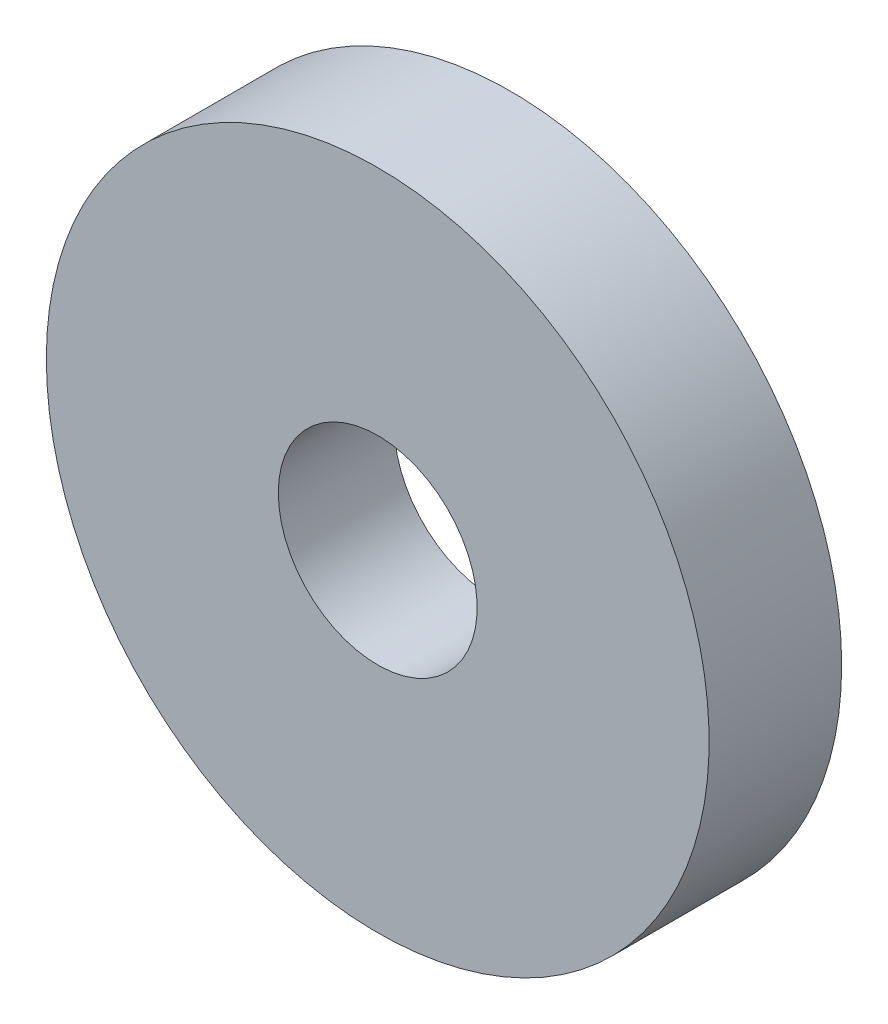
SolidWorks part; units mm, degrees
material "AISI 1020"
ref_plane "Спереди" through (0, 0, 0) normal (0, 0, 1) x (1, 0, 0)
ref_plane "Сверху" through (0, 0, 0) normal (0, 1, 0) x (1, 0, 0)
ref_plane "Справа" through (0, 0, 0) normal (1, 0, 0) x (0, 0, -1)
sketch "Эскиз1" plane through (0, 0, 0) normal (0, 0, 1) x (1, 0, 0)
  circle A0 centre (0, 0) radius 7.9 construction
  circle A1 centre (0, 0) radius 7.9
  circle A2 centre (0, 0) radius 20
  arc A3 (19.3591, 5.0223) -> (-19.3591, 5.0223) centre (0, 0) ccw construction
extrude "Бобышка-Вытянуть1" add sketch "Эскиз1" along normal up to surface (1 mm away)
sketch "Эскиз2" plane through (0, 0, 1) normal (0, 0, 1) x (1, 0, 0)
  circle A0 centre (0, 0) radius 6 construction
  circle A1 centre (0, 0) radius 6
  circle A2 centre (0, 0) radius 20 construction
  circle A3 centre (0, 0) radius 20
extrude "Бобышка-Вытянуть2" add sketch "Эскиз2" along normal offset from surface (7 mm away) 1
